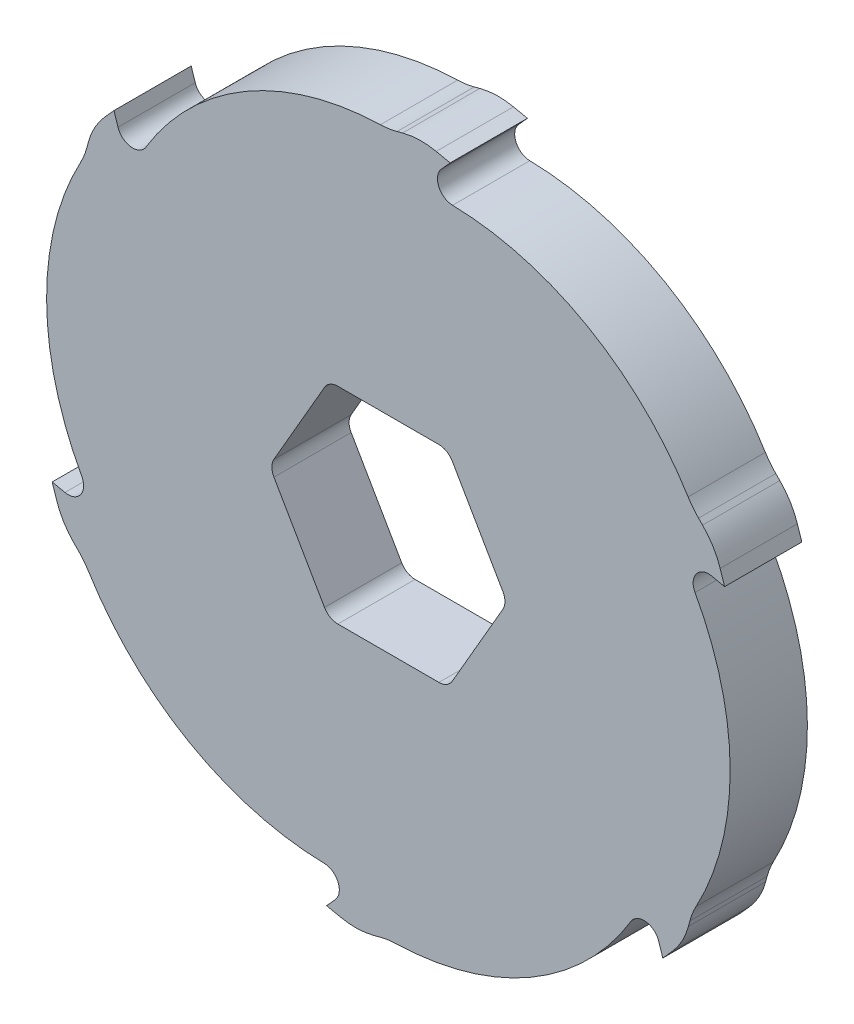
SolidWorks part; units mm, degrees
ref_plane "Front Plane" through (0, 0, 0) normal (0, 0, 1) x (1, 0, 0)
ref_plane "Top Plane" through (0, 0, 0) normal (0, 1, 0) x (1, 0, 0)
ref_plane "Right Plane" through (0, 0, 0) normal (1, 0, 0) x (0, 0, -1)
sketch "Sketch1" plane through (0, 0, 0) normal (0, 0, 1) x (1, 0, 0)
  line L1 (22.228, 1.5) -> (12.413, 18.5)
  line L2 (9.815, 20) -> (-9.815, 20)
  line L3 (-12.413, 18.5) -> (-22.228, 1.5)
  line L4 (-22.228, -1.5) -> (-12.413, -18.5)
  line L5 (-9.815, -20) -> (9.815, -20)
  line L6 (12.413, -18.5) -> (22.228, -1.5)
  circle A0 centre (0, 0) radius 70
  circle A1 centre (0, 0) radius 20 construction
  arc A2 (-22.228, 1.5) -> (-22.228, -1.5) centre (-19.6299, 0) ccw
  arc A3 (-12.413, -18.5) -> (-9.815, -20) centre (-9.815, -17) ccw
  arc A4 (9.815, -20) -> (12.413, -18.5) centre (9.815, -17) ccw
  arc A5 (22.228, 1.5) -> (22.228, -1.5) centre (19.6299, 0) cw
  arc A6 (12.413, 18.5) -> (9.815, 20) centre (9.815, 17) ccw
  arc A7 (-9.815, 20) -> (-12.413, 18.5) centre (-9.815, 17) ccw
  dimension "D1" = 140
  dimension "D2" = 40
  dimension "D3" = 3
extrude "Boss-Extrude1" add sketch "Sketch1" along normal mid plane 15
sketch "Sketch2" plane through (0, 0, 7.5) normal (0, 0, 1) x (1, 0, 0)
  line L0 (0, 68.1347) -> (6, 69.7424)
  line L1 (0, -8.25) -> (0, 8.25) construction
  line L2 (6, 69.7424) -> (12, 68.467)
  line L3 (12, 68.467) -> (5.5253, 61.2761)
  line L4 (59.0064, 34.0673) -> (63.3987, 29.675)
  line L5 (63.3987, 29.675) -> (65.2942, 23.8412)
  line L6 (65.2942, 23.8412) -> (55.8293, 25.853)
  line L7 (59.0064, -34.0673) -> (57.3987, -40.0673)
  line L8 (57.3987, -40.0673) -> (53.2942, -44.6258)
  line L9 (53.2942, -44.6258) -> (50.304, -35.4231)
  line L10 (0, -68.1347) -> (-6, -69.7424)
  line L11 (-6, -69.7424) -> (-12, -68.467)
  line L12 (-12, -68.467) -> (-5.5253, -61.2761)
  line L13 (-59.0064, -34.0673) -> (-63.3987, -29.675)
  line L14 (-63.3987, -29.675) -> (-65.2942, -23.8412)
  line L15 (-65.2942, -23.8412) -> (-55.8293, -25.853)
  line L16 (-59.0064, 34.0673) -> (-57.3987, 40.0673)
  line L17 (-57.3987, 40.0673) -> (-53.2942, 44.6258)
  line L18 (-53.2942, 44.6258) -> (-50.304, 35.4231)
  circle A0 centre (0, 0) radius 70 construction
  arc A1 (0, 68.1347) -> (-50.304, 35.4231) centre (0, 13.1) ccw
  arc A2 (59.0064, 34.0673) -> (5.5253, 61.2761) centre (11.3449, 6.55) ccw
  arc A3 (59.0064, -34.0673) -> (55.8293, 25.853) centre (11.3449, -6.55) ccw
  arc A4 (0, -68.1347) -> (50.304, -35.4231) centre (0, -13.1) ccw
  arc A5 (-59.0064, -34.0673) -> (-1.3447, -60.6685) centre (-11.3449, -6.55) ccw
  arc A6 (-59.0064, 34.0673) -> (-55.8293, -25.853) centre (-11.3449, 6.55) ccw
  circle A7 centre (0, 0) radius 70
  point P44 (0, 0)
  circle M4 centre (0, 0) radius 70
  dimension "D7" = 55.0347
  dimension "D1" = 78
  dimension "D2" = 6
  dimension "D3" = 12
  dimension "D4" = 120
  dimension "D5" = 105
  dimension "D6" = 13.1
  dimension "D8" = 6
extrude "Cut-Extrude1" cut sketch "Sketch2" against normal blind 15 contours A2 L4 L2 L3 M4 | A1 L0 L17 L18 M4 | A6 L16 L14 L15 M4 | A5 L13 L11 L12 M4 | A4 L10 L8 L9 M4 | A3 L7 L5 L6 M4
fillet "Fillet1" radius 14 12 edges at (63.3987, 29.675, 0) (59.0064, 34.0673, 0) (59.0064, -34.0673, 0) (57.3987, -40.0673, 0) (0, -68.1347, 0) (-6, -69.7424, 0) (-63.3987, -29.675, 0) (-59.0064, -34.0673, 0) (-59.0064, 34.0673, 0) (-57.3987, 40.0673, 0) (0, 68.1347, 0) (6, 69.7424, 0)
fillet "Fillet2" radius 3 6 edges at (-50.304, 35.4231, 0) (50.304, -35.4231, 0) (-5.5253, -61.2761, 0) (-55.8293, -25.853, 0) (5.5253, 61.2761, 0) (55.8293, 25.853, 0)
